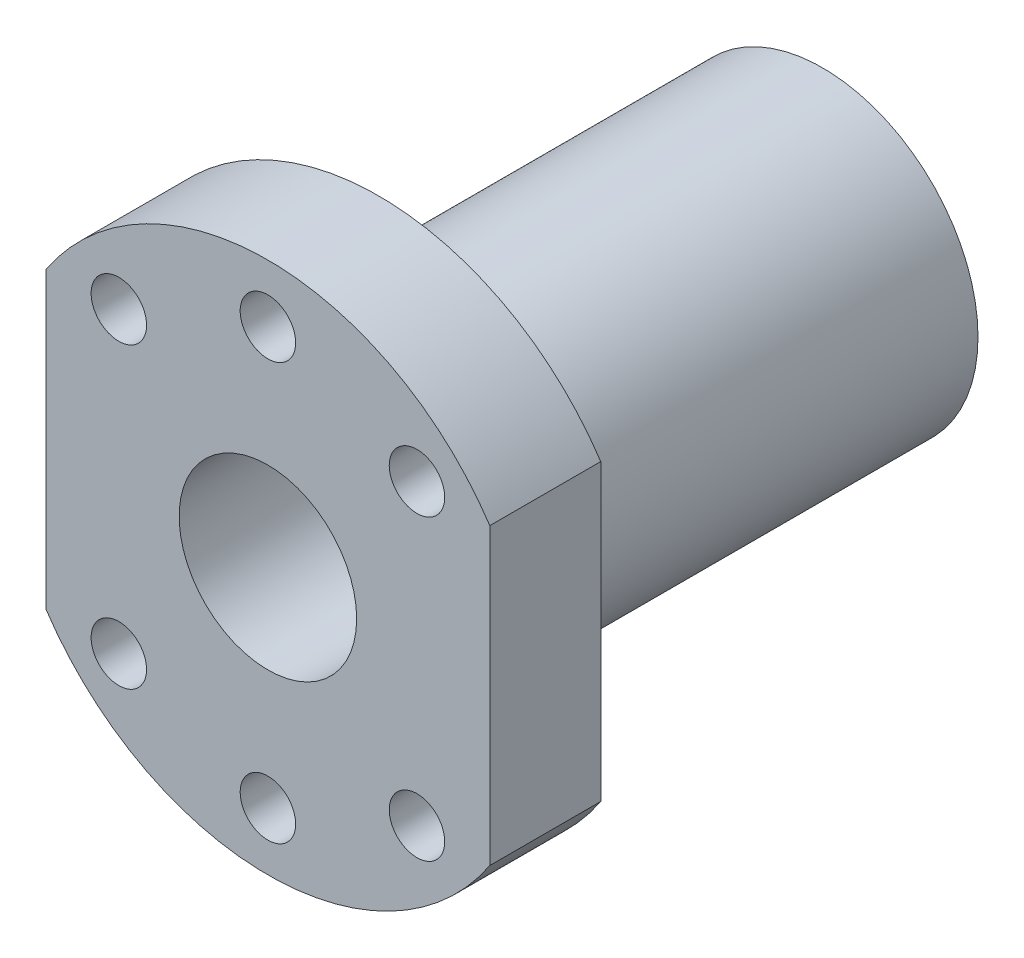
SolidWorks part; units mm, degrees
ref_plane "Piano frontale" through (0, 0, 0) normal (0, 0, 1) x (1, 0, 0)
ref_plane "Piano superiore" through (0, 0, 0) normal (0, 1, 0) x (1, 0, 0)
ref_plane "Piano destro" through (0, 0, 0) normal (1, 0, 0) x (0, 0, -1)
sketch "Schizzo1" plane through (0, 0, 0) normal (0, 0, 1) x (1, 0, 0)
  line L0 (0, 0) -> (-33.4653, 33.4653) construction
  line L1 (0, 0) -> (-48.3841, 0) construction
  line L2 (20, -13.2665) -> (20, 13.2665)
  line L3 (0, 0) -> (0, 37.5637) construction
  line L4 (-20, -13.2665) -> (-20, 13.2665)
  line L5 (20, -37.5637) -> (-20, 37.5637) construction
  line L6 (20, 37.5637) -> (-20, -37.5637) construction
  arc A0 (-20, -13.2665) -> (20, -13.2665) centre (0, 0) ccw
  arc A1 (20, 13.2665) -> (-20, 13.2665) centre (0, 0) ccw
  circle A2 centre (0, 0) radius 8
  circle A3 centre (-13.435, 13.435) radius 2.5
  circle A4 centre (0, 0) radius 19 construction
  circle A5 centre (13.435, 13.435) radius 2.5
  circle A6 centre (13.435, -13.435) radius 2.5
  circle A7 centre (-13.435, -13.435) radius 2.5
  circle A8 centre (0, 18.7819) radius 2.5
  circle A9 centre (0, -18.7819) radius 2.5
  dimension "D1" = 48
  dimension "D3" = 16
  dimension "D5" = 38
  dimension "D6" = 5
  dimension "D2" = 40
  dimension "D4" = 45
extrude "Estrusione-Estrusione1" add sketch "Schizzo1" against normal blind 50
sketch "Schizzo2" plane through (0, 0, -50) normal (0, 0, -1) x (-1, 0, 0)
  circle A0 centre (0, 0) radius 14
  dimension "D1" = 28
extrude "Taglio-Estrusione1" cut sketch "Schizzo2" against normal blind 40 flip side to cut
